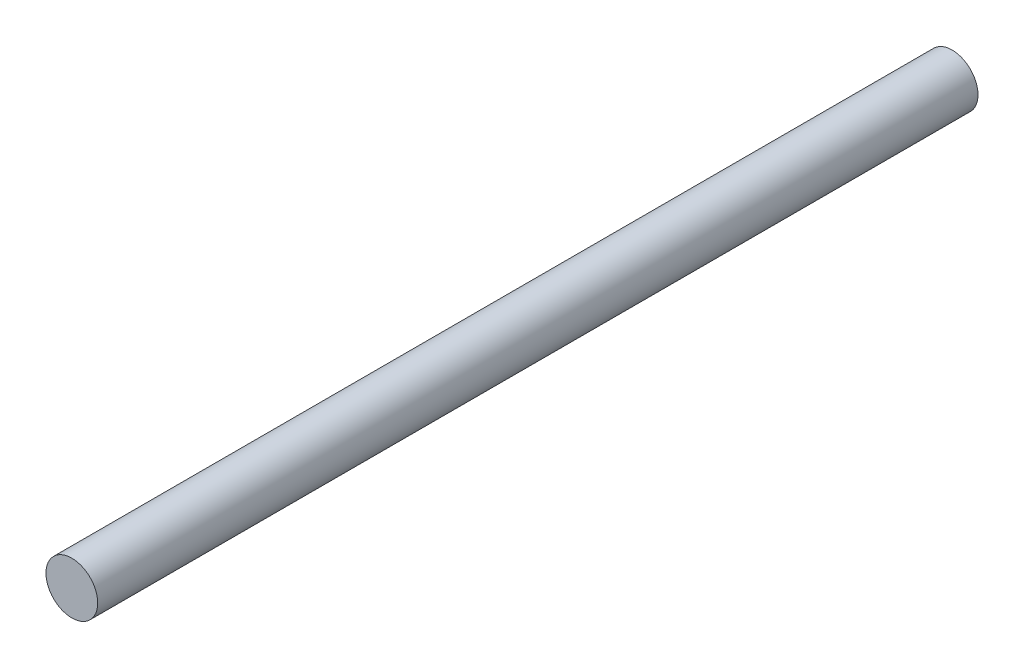
SolidWorks part; units mm, degrees
ref_plane "Front Plane" through (0, 0, 0) normal (0, 0, 1) x (1, 0, 0)
ref_plane "Top Plane" through (0, 0, 0) normal (0, 1, 0) x (1, 0, 0)
ref_plane "Right Plane" through (0, 0, 0) normal (1, 0, 0) x (0, 0, -1)
sketch "Sketch1" plane through (0, 0, 0) normal (0, 0, 1) x (1, 0, 0)
  circle A0 centre (0, 0) radius 6.35
extrude "Boss-Extrude1" add sketch "Sketch1" along normal blind 215.9
